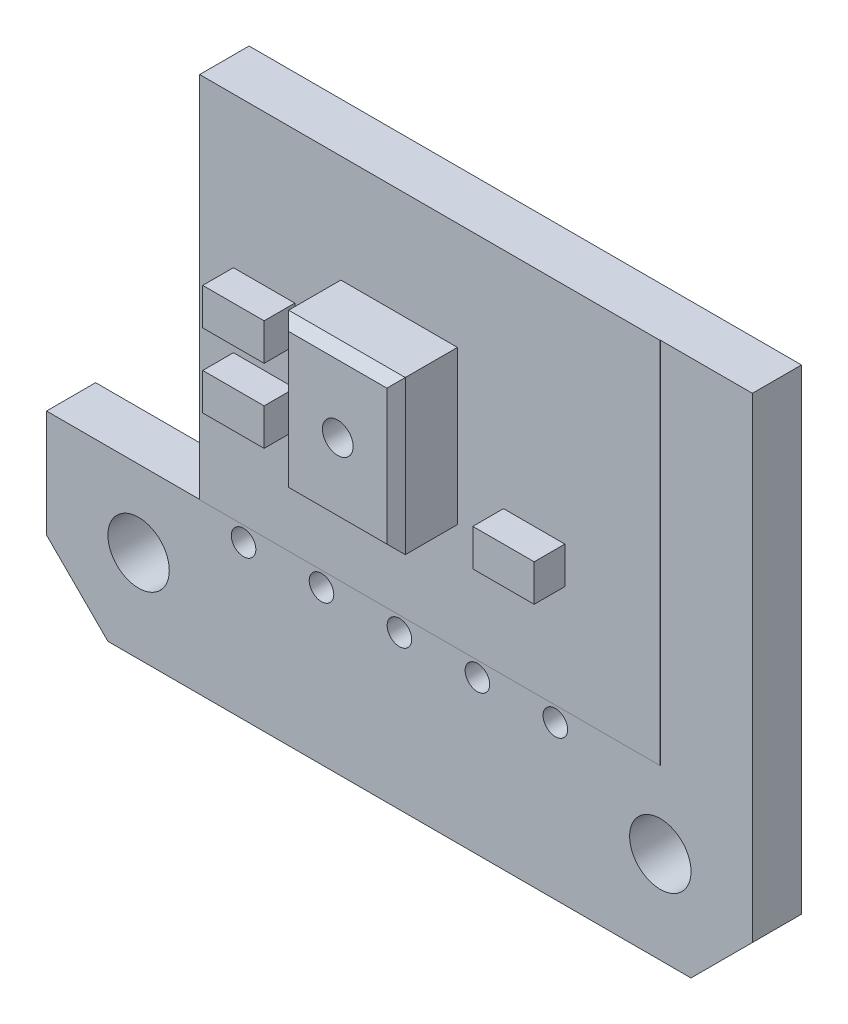
SolidWorks part; units mm, degrees
ref_plane "Front Plane" through (0, 0, 0) normal (0, 0, 1) x (1, 0, 0)
ref_plane "Top Plane" through (0, 0, 0) normal (0, 1, 0) x (1, 0, 0)
ref_plane "Right Plane" through (0, 0, 0) normal (1, 0, 0) x (0, 0, -1)
sketch "Sketch1" plane through (0, 0, 0) normal (0, 0, 1) x (1, 0, 0)
  line L0 (-11.5, 9.5) -> (-9.5, 11.5)
  line L1 (-9.5, -11.5) -> (9.5, -11.5)
  line L2 (-11.5, -9.5) -> (-11.5, 9.5)
  line L3 (-9.5, 11.5) -> (9.5, 11.5)
  line L4 (11.5, -9.5) -> (11.5, 9.5)
  line L7 (9.5, 11.5) -> (11.5, 9.5)
  line L8 (9.5, -11.5) -> (11.5, -9.5)
  line L9 (-11.5, -9.5) -> (-9.5, -11.5)
  line L11 (-9, -6) -> (9, -6) construction
  line L12 (-9, -6) -> (-9, 6) construction
  line L13 (-9, 6) -> (9, 6) construction
  line L14 (9, -6) -> (9, 6) construction
  point P0 (0, 0)
  point P1 (0, 11.5)
  point P4 (0, -6)
  point P14 (9, 0)
  point P22 (0, 0)
  dimension "D1" = 23
  dimension "D2" = 23
  dimension "D3" = 2
  dimension "D5" = 2
  dimension "D6" = 11.5
  dimension "D7" = 12
  dimension "D8" = 2.5
extrude "Boss-Extrude1" add sketch "Sketch1" along normal blind 1.6
sketch "Sketch2" plane through (0, 0, 0) normal (0, 0, 1) x (1, 0, 0)
  line L0 (11.5, -9.5) -> (11.5, 9.5) construction
  line L1 (-8.5, -6) -> (8.5, -6)
  line L2 (-8.5, -6) -> (-8.5, 6)
  line L3 (-8.5, 6) -> (8.5, 6)
  line L4 (8.5, -6) -> (8.5, 6)
  line L5 (-8.5, -6) -> (8.5, 6) construction
  line L6 (-8.5, 6) -> (8.5, -6) construction
  line L7 (-9.5, -11.5) -> (9.5, -11.5) construction
  point P0 (0, 0)
  dimension "D1" = 3
  dimension "D2" = 5.5
extrude "Boss-Extrude2" add sketch "Sketch2" along normal blind 1.61
sketch "Sketch3" plane through (0, 0, 0) normal (0, 0, 1) x (1, 0, 0)
  line L0 (0, -5.3) -> (0, -7.7) construction
  line L1 (-7, -7.7) -> (7, -7.7)
  line L2 (-7, -7.7) -> (-7, -5.3)
  line L3 (-7, -5.3) -> (7, -5.3)
  line L4 (7, -7.7) -> (7, -5.3)
  line L5 (-7, -7.7) -> (7, -5.3) construction
  line L6 (-7, -5.3) -> (7, -7.7) construction
  line L7 (-6.8, -5.5) -> (6.8, -5.5)
  line L8 (6.8, -7.5) -> (6.8, -5.5)
  line L9 (-6.8, -7.5) -> (6.8, -7.5)
  line L10 (-6.8, -7.5) -> (-6.8, -5.5)
  circle A0 centre (0, -6.5) radius 0.6
  circle A1 centre (2.54, -6.5) radius 0.6
  circle A2 centre (5.08, -6.5) radius 0.6
  circle A3 centre (-5.08, -6.5) radius 0.6
  circle A4 centre (-2.54, -6.5) radius 0.6
  circle A5 centre (-5.08, -6.5) radius 0.4
  circle A6 centre (-2.54, -6.5) radius 0.4
  circle A7 centre (0, -6.5) radius 0.4
  circle A8 centre (2.54, -6.5) radius 0.4
  circle A9 centre (5.08, -6.5) radius 0.4
  point P0 (0, -6.5)
  dimension "D6" = 1.2
  dimension "D1" = 14
  dimension "D2" = 2.4
  dimension "D3" = 6.5
  dimension "D4" = 2.54
  dimension "D5" = 2.54
  dimension "D7" = 0.2
extrude "Cut-Extrude1" cut sketch "Sketch3" along normal blind 2.62 contours A5 | A6 | A7 | A8 | A9
sketch "Sketch4" plane through (0, 0, 0) normal (0, 0, 1) x (1, 0, 0)
  line L1 (-1.9, -2.5) -> (1.9, -2.5)
  line L2 (-1.9, -2.5) -> (-1.9, 2.5)
  line L3 (-1.9, 2.5) -> (1.9, 2.5)
  line L4 (1.9, -2.5) -> (1.9, 2.5)
  line L5 (-1.9, -2.5) -> (1.9, 2.5) construction
  line L6 (-1.9, 2.5) -> (1.9, -2.5) construction
  point P0 (0, 0)
  dimension "D1" = 5
  dimension "D2" = 3.8
extrude "Boss-Extrude4" add sketch "Sketch4" along normal blind 2 from surface at 1.61 starting at face at (0, 0, 1.61)
sketch "Sketch5" plane through (0, 0, 0) normal (0, 0, 1) x (1, 0, 0)
  line L1 (-5.4, -1.3) -> (-3.4, -1.3)
  line L2 (-5.4, -1.3) -> (-5.4, -2.5)
  line L3 (-5.4, -2.5) -> (-3.4, -2.5)
  line L4 (-3.4, -1.3) -> (-3.4, -2.5)
  line L5 (-5.4, -1.3) -> (-3.4, -2.5) construction
  line L6 (-5.4, -2.5) -> (-3.4, -1.3) construction
  line L7 (-5.4, 1.1) -> (-3.4, 1.1)
  line L8 (-5.4, 1.1) -> (-5.4, -0.1)
  line L9 (-5.4, -0.1) -> (-3.4, -0.1)
  line L10 (-3.4, 1.1) -> (-3.4, -0.1)
  line L11 (-5.4, 1.1) -> (-3.4, -0.1) construction
  line L12 (-5.4, -0.1) -> (-3.4, 1.1) construction
  line L13 (3.4, -1.3) -> (5.4, -1.3)
  line L14 (3.4, -1.3) -> (3.4, -2.5)
  line L15 (3.4, -2.5) -> (5.4, -2.5)
  line L16 (5.4, -1.3) -> (5.4, -2.5)
  line L17 (3.4, -1.3) -> (5.4, -2.5) construction
  line L18 (3.4, -2.5) -> (5.4, -1.3) construction
  line L19 (1.9, -2.5) -> (1.9, 2.5) construction
  line L20 (-1.9, 2.5) -> (-1.9, -2.5) construction
  line L21 (-1.9, -2.5) -> (1.9, -2.5) construction
  point P0 (-4.4, -1.9)
  point P5 (-4.4, 0.5)
  point P10 (4.4, -1.9)
  dimension "D1" = 1.2
  dimension "D2" = 2
  dimension "D3" = 1.5
  dimension "D4" = 1.5
  dimension "D5" = 1.2
extrude "Boss-Extrude5" add sketch "Sketch5" along normal blind 1 from surface at 1.61 starting at face at (0, 0, 1.61)
chamfer "Chamfer1" distance 0.3 angle 45 4 edges at (0, -2.5, 3.61) (-1.9, 0, 3.61) (0, 2.5, 3.61) (1.9, 0, 3.61)
sketch "Sketch8" plane through (0, 0, 0) normal (0, 0, 1) x (1, 0, 0)
  line L1 (8.5, 8.5) -> (-8.5, 8.5) construction
  line L2 (8.5, 8.5) -> (8.5, -8.5) construction
  line L3 (8.5, -8.5) -> (-8.5, -8.5) construction
  line L4 (-8.5, 8.5) -> (-8.5, -8.5) construction
  line L5 (8.5, 8.5) -> (-8.5, -8.5) construction
  line L6 (8.5, -8.5) -> (-8.5, 8.5) construction
  circle A0 centre (8.5, -8.5) radius 1
  circle A1 centre (-8.5, -8.5) radius 1
  circle A2 centre (8.5, 8.5) radius 1
  circle A3 centre (-8.5, 8.5) radius 1
  point P0 (0, 0)
  dimension "D3" = 2
  dimension "D1" = 17
  dimension "D2" = 17
extrude "Cut-Extrude2" cut sketch "Sketch8" against normal mid plane 7
sketch "Sketch9" plane through (0, 0, 0) normal (0, 0, 1) x (1, 0, 0)
  line L0 (11.5, -9.5) -> (11.5, 9.5) construction
  line L1 (11.5, 6) -> (-11.5, 6)
  line L2 (11.5, 6) -> (11.5, 11.5)
  line L3 (11.5, 11.5) -> (-11.5, 11.5)
  line L4 (-11.5, 6) -> (-11.5, 11.5)
  line L5 (-11.5, 9.5) -> (-11.5, -9.5) construction
  line L6 (-8.5, 6) -> (8.5, 6) construction
  line L7 (9.5, 11.5) -> (-9.5, 11.5) construction
extrude "Cut-Extrude3" cut sketch "Sketch9" against normal mid plane 7
sketch "Sketch10" plane through (0, 0, 0) normal (0, 0, 1) x (1, 0, 0)
  line L0 (-8.5, -6) -> (8.5, -6) construction
  line L1 (-6.5, 6) -> (-11.5, 6)
  line L2 (-6.5, 6) -> (-6.5, -6)
  line L3 (-6.5, -6) -> (-11.5, -6)
  line L4 (-11.5, 6) -> (-11.5, -6)
  dimension "D1" = 5
extrude "Cut-Extrude4" cut sketch "Sketch10" against normal mid plane 7
sketch "Sketch11" plane through (0, 0, 0) normal (0, 0, 1) x (1, 0, 0)
  circle A0 centre (0, 0) radius 0.5
  dimension "D1" = 1
extrude "Cut-Extrude5" cut sketch "Sketch11" against normal mid plane 10
